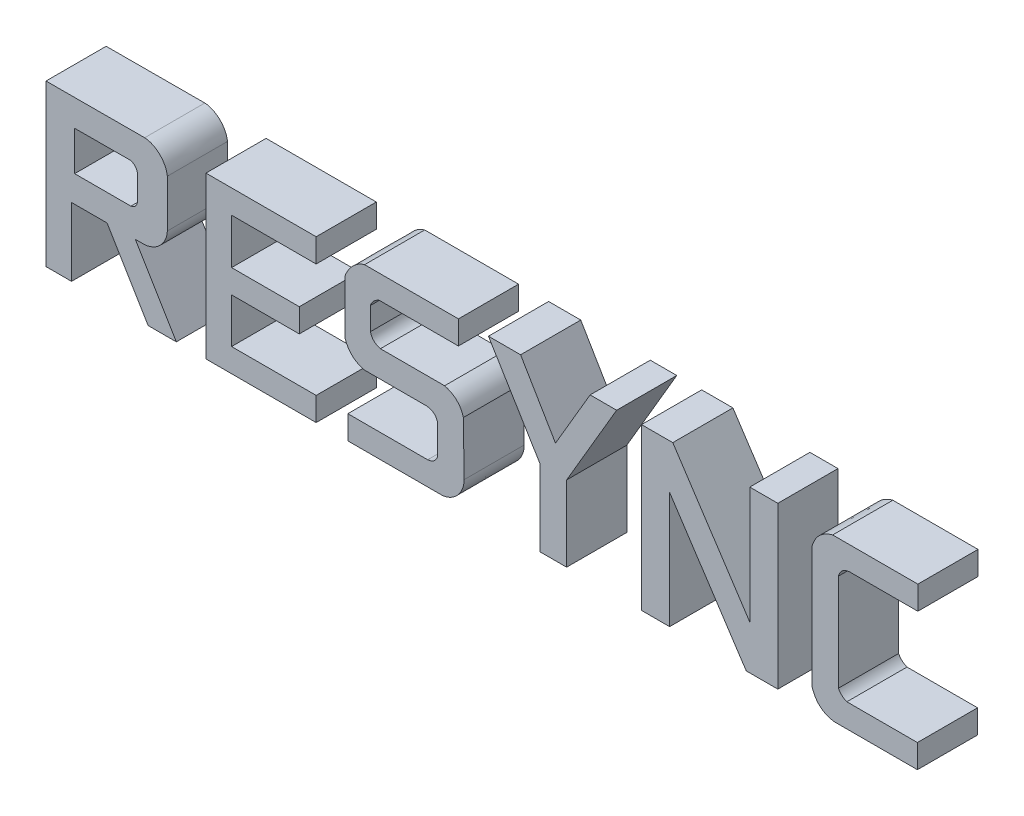
SolidWorks part; units mm, degrees
ref_plane "Front Plane" through (0, 0, 0) normal (0, 0, 1) x (1, 0, 0)
ref_plane "Top Plane" through (0, 0, 0) normal (0, 1, 0) x (1, 0, 0)
ref_plane "Right Plane" through (0, 0, 0) normal (1, 0, 0) x (0, 0, -1)
sketch "Sketch39" plane through (0, 0, 0) normal (0, 0, 1) x (1, 0, 0)
  line L0 (147.6667, 279.75) -> (830.3333, 279.75) construction
  line L1 (297, 531.75) -> (1577, 531.75) construction
  line L2 (-15.0225, 6.9502) -> (-15.0225, 1.4057)
  line L3 (-15.0225, 1.4057) -> (-13.9728, 1.4057)
  line L4 (-13.9728, 1.4057) -> (-13.9728, 3.6779)
  line L5 (-13.9728, 3.6779) -> (-12.9478, 3.6779)
  line L6 (-12.9478, 3.6779) -> (-11.5831, 1.4057)
  line L7 (-11.5831, 1.4057) -> (-10.4121, 1.4057)
  line L8 (-10.4121, 1.4057) -> (-11.7768, 3.6779)
  line L9 (-11.7768, 3.6779) -> (-11.6385, 3.6779)
  line L10 (-10.7883, 4.5476) -> (-10.7883, 6.1322)
  line L11 (-11.6385, 6.9576) -> (-15.0225, 6.9502)
  line L12 (-13.9728, 5.9647) -> (-13.9699, 4.6587)
  line L13 (-13.9699, 4.6587) -> (-12.0989, 4.6587)
  line L14 (-11.885, 4.8692) -> (-11.885, 5.7351)
  line L15 (-12.1205, 5.972) -> (-13.9728, 5.9647)
  line L16 (-9.7048, 6.9576) -> (-9.7048, 1.4057)
  line L17 (-9.7048, 1.4057) -> (-5.8401, 1.4057)
  line L18 (-5.8401, 1.4057) -> (-5.8401, 2.3891)
  line L19 (-5.8401, 2.3891) -> (-8.6526, 2.3891)
  line L20 (-8.6526, 2.3891) -> (-8.6526, 3.6779)
  line L21 (-8.6526, 3.6779) -> (-6.4009, 3.6779)
  line L22 (-6.4009, 3.6779) -> (-6.4009, 4.6624)
  line L23 (-6.4009, 4.6624) -> (-8.6526, 4.6624)
  line L24 (-8.6526, 4.6624) -> (-8.6526, 5.972)
  line L25 (-8.6526, 5.972) -> (-5.8401, 5.972)
  line L26 (-5.8401, 5.972) -> (-5.8401, 6.9576)
  line L27 (-5.8401, 6.9576) -> (-9.7048, 6.9576)
  line L28 (-4.9866, 1.4057) -> (-1.7436, 1.4057)
  line L29 (-0.9222, 2.3209) -> (-0.9432, 4.116)
  line L30 (-1.6562, 4.8018) -> (-3.7908, 4.8018)
  line L31 (-4.0366, 5.0385) -> (-4.0366, 5.7632)
  line L32 (-3.8276, 5.976) -> (-1.1096, 5.976)
  line L33 (-1.1096, 5.976) -> (-1.1096, 6.9576)
  line L34 (-1.1096, 6.9576) -> (-4.3432, 6.9576)
  line L35 (-5.0828, 6.2212) -> (-5.0828, 4.4143)
  line L36 (-4.3432, 3.7217) -> (-2.2708, 3.7217)
  line L37 (-1.9972, 3.5013) -> (-1.9972, 2.5759)
  line L38 (-2.2357, 2.3891) -> (-4.9866, 2.3891)
  line L39 (-4.9866, 2.3891) -> (-4.9866, 1.4057)
  line L40 (-0.3891, 6.9576) -> (1.3981, 4.0225)
  line L41 (1.3981, 4.0225) -> (1.3981, 1.4057)
  line L42 (1.3981, 1.4057) -> (2.4881, 1.4057)
  line L43 (2.4881, 1.4057) -> (2.4881, 3.9919)
  line L44 (2.4881, 3.9919) -> (4.2251, 6.9576)
  line L45 (4.2251, 6.9576) -> (3.1117, 6.9576)
  line L46 (3.1117, 6.9576) -> (2.0173, 5.0892)
  line L47 (2.0173, 5.0892) -> (0.9145, 6.9576)
  line L48 (0.9145, 6.9576) -> (-0.3891, 6.9576)
  line L49 (4.7787, 6.9576) -> (4.7787, 1.4057)
  line L50 (4.7787, 1.4057) -> (5.9124, 1.4057)
  line L51 (5.9124, 1.4057) -> (5.9124, 5.0385)
  line L52 (5.9124, 5.0385) -> (8.3065, 1.4057)
  line L53 (8.3065, 1.4057) -> (9.5107, 1.4057)
  line L54 (9.5107, 1.4057) -> (9.5107, 6.9576)
  line L55 (9.5107, 6.9576) -> (8.377, 6.9576)
  line L56 (8.377, 6.9576) -> (8.377, 3.307)
  line L57 (8.377, 3.307) -> (5.971, 6.9576)
  line L58 (5.971, 6.9576) -> (4.7787, 6.9576)
  line L59 (11.2204, 6.9576) -> (14.1659, 6.9576)
  line L60 (14.1659, 6.9576) -> (14.1659, 5.976)
  line L61 (14.1659, 5.976) -> (11.8028, 5.976)
  line L62 (11.525, 5.7538) -> (11.525, 2.5629)
  line L63 (11.7216, 2.3891) -> (14.1513, 2.3891)
  line L64 (14.1513, 2.3891) -> (14.1513, 1.4057)
  line L65 (14.1513, 1.4057) -> (11.2756, 1.4057)
  line L66 (10.4471, 2.1356) -> (10.4471, 6.2043)
  line L67 (-11.6412, 6.8576) -> (-14.9225, 6.8504)
  line L68 (-14.9225, 6.8504) -> (-14.9225, 1.5057)
  line L69 (-14.9225, 1.5057) -> (-14.0728, 1.5057)
  line L70 (-14.0728, 1.5057) -> (-14.0728, 3.7779)
  line L71 (-14.0728, 3.7779) -> (-12.8913, 3.7779)
  line L72 (-12.8913, 3.7779) -> (-11.5265, 1.5057)
  line L73 (-11.5265, 1.5057) -> (-10.5888, 1.5057)
  line L74 (-10.5888, 1.5057) -> (-11.9535, 3.7779)
  line L75 (-11.9535, 3.7779) -> (-11.6421, 3.7779)
  line L76 (-10.8883, 4.5493) -> (-10.8883, 6.127)
  line L77 (-5.9401, 6.8576) -> (-9.6048, 6.8576)
  line L78 (-9.6048, 6.8576) -> (-9.6048, 1.5057)
  line L79 (-9.6048, 1.5057) -> (-5.9401, 1.5057)
  line L80 (-5.9401, 1.5057) -> (-5.9401, 2.2891)
  line L81 (-5.9401, 2.2891) -> (-8.7526, 2.2891)
  line L82 (-8.7526, 2.2891) -> (-8.7526, 3.7779)
  line L83 (-8.7526, 3.7779) -> (-6.5009, 3.7779)
  line L84 (-6.5009, 3.7779) -> (-6.5009, 4.5624)
  line L85 (-6.5009, 4.5624) -> (-8.7526, 4.5624)
  line L86 (-8.7526, 4.5624) -> (-8.7526, 6.072)
  line L87 (-8.7526, 6.072) -> (-5.9401, 6.072)
  line L88 (-5.9401, 6.072) -> (-5.9401, 6.8576)
  line L89 (-1.8972, 3.5143) -> (-1.8972, 2.5596)
  line L90 (-2.2312, 2.2891) -> (-4.8866, 2.2891)
  line L91 (-4.8866, 2.2891) -> (-4.8866, 1.5057)
  line L92 (-4.8866, 1.5057) -> (-1.7478, 1.5057)
  line L93 (-1.0222, 2.3197) -> (-1.0431, 4.101)
  line L94 (-1.6691, 4.7018) -> (-3.8035, 4.7018)
  line L95 (-4.1366, 5.0243) -> (-4.1366, 5.7792)
  line L96 (-3.845, 6.076) -> (-1.2096, 6.076)
  line L97 (-1.2096, 6.076) -> (-1.2096, 6.8576)
  line L98 (-1.2096, 6.8576) -> (-4.3307, 6.8576)
  line L99 (-4.9828, 6.2047) -> (-4.9828, 4.4296)
  line L100 (-4.3314, 3.8217) -> (-2.2675, 3.8217)
  line L101 (0.8574, 6.8576) -> (-0.2112, 6.8576)
  line L102 (-0.2112, 6.8576) -> (1.4981, 4.0505)
  line L103 (1.4981, 4.0505) -> (1.4981, 1.5057)
  line L104 (1.4981, 1.5057) -> (2.3881, 1.5057)
  line L105 (2.3881, 1.5057) -> (2.3881, 4.019)
  line L106 (2.3881, 4.019) -> (4.0506, 6.8576)
  line L107 (4.0506, 6.8576) -> (3.169, 6.8576)
  line L108 (3.169, 6.8576) -> (2.0177, 4.8919)
  line L109 (2.0177, 4.8919) -> (0.8574, 6.8576)
  line L110 (5.9172, 6.8576) -> (4.8787, 6.8576)
  line L111 (4.8787, 6.8576) -> (4.8787, 1.5057)
  line L112 (4.8787, 1.5057) -> (5.8124, 1.5057)
  line L113 (5.8124, 1.5057) -> (5.8124, 5.372)
  line L114 (5.8124, 5.372) -> (8.3604, 1.5057)
  line L115 (8.3604, 1.5057) -> (9.4107, 1.5057)
  line L116 (9.4107, 1.5057) -> (9.4107, 6.8576)
  line L117 (9.4107, 6.8576) -> (8.477, 6.8576)
  line L118 (8.477, 6.8576) -> (8.477, 2.9735)
  line L119 (8.477, 2.9735) -> (5.9172, 6.8576)
  line L120 (11.2332, 6.8576) -> (14.0659, 6.8576)
  line L121 (14.0659, 6.8576) -> (14.0659, 6.076)
  line L122 (14.0659, 6.076) -> (11.7997, 6.076)
  line L123 (11.425, 5.7674) -> (11.425, 2.5393)
  line L124 (11.7046, 2.2891) -> (14.0513, 2.2891)
  line L125 (14.0513, 2.2891) -> (14.0513, 1.5057)
  line L126 (14.0513, 1.5057) -> (11.2829, 1.5057)
  line L127 (10.5471, 2.1506) -> (10.5471, 6.1901)
  spline S0 degree 3 poles (-11.6385, 3.6779) (-11.1992, 3.7086) (-10.8033, 4.0794) (-10.7883, 4.5476) knots 0 0 0 0 1 1 1 1
  spline S1 degree 3 poles (-10.7883, 6.1322) (-10.8311, 6.5559) (-11.2076, 6.9342) (-11.6385, 6.9576) knots 0 0 0 0 1 1 1 1
  spline S2 degree 2 poles (-12.0989, 4.6587) (-11.9219, 4.6939) (-11.885, 4.8692) knots 0 0 0 1 1 1
  spline S3 degree 2 poles (-11.885, 5.7351) (-11.9286, 5.9229) (-12.1205, 5.972) knots 0 0 0 1 1 1
  spline S4 degree 3 poles (-1.7436, 1.4057) (-1.3804, 1.4351) (-0.9949, 1.7823) (-0.9211, 2.2256) (-0.9222, 2.3209) knots 0 0 0 0 0.786572 1 1 1 1
  spline S5 degree 2 poles (-0.9432, 4.116) (-1.0994, 4.659) (-1.6562, 4.8018) knots 0 0 0 1 1 1
  spline S6 degree 2 poles (-3.7908, 4.8018) (-3.9821, 4.8512) (-4.0366, 5.0385) knots 0 0 0 1 1 1
  spline S7 degree 2 poles (-4.0366, 5.7632) (-3.9851, 5.9195) (-3.8276, 5.976) knots 0 0 0 1 1 1
  spline S8 degree 3 poles (-4.3432, 6.9576) (-4.7111, 6.8668) (-4.9695, 6.562) (-5.0828, 6.2212) knots 0 0 0 0 1 1 1 1
  spline S9 degree 2 poles (-5.0828, 4.4143) (-4.911, 3.8544) (-4.3432, 3.7217) knots 0 0 0 1 1 1
  spline S10 degree 2 poles (-2.2708, 3.7217) (-2.0516, 3.7069) (-1.9972, 3.5013) knots 0 0 0 1 1 1
  spline S11 degree 2 poles (-1.9972, 2.5759) (-2.0542, 2.4054) (-2.2357, 2.3891) knots 0 0 0 1 1 1
  spline S12 degree 2 poles (11.8028, 5.976) (11.5825, 5.9623) (11.525, 5.7538) knots 0 0 0 1 1 1
  spline S13 degree 2 poles (11.525, 2.5629) (11.5888, 2.4355) (11.7216, 2.3891) knots 0 0 0 1 1 1
  spline S14 degree 2 poles (11.2756, 1.4057) (10.6391, 1.4971) (10.4471, 2.1356) knots 0 0 0 1 1 1
  spline S15 degree 2 poles (10.4471, 6.2043) (10.6161, 6.8025) (11.2204, 6.9576) knots 0 0 0 1 1 1
  spline S16 degree 1 poles (-11.6421, 3.7779) (-10.8883, 4.5493) knots 0 0 1 1 construction
  spline S17 degree 1 poles (-10.8883, 6.127) (-11.6412, 6.8576) knots 0 0 1 1 construction
  spline S18 degree 3 poles (-11.6421, 3.7779) (-11.452, 3.792) (-11.0748, 3.9663) (-10.8949, 4.3563) (-10.8883, 4.5493) knots 0.002907 0.002907 0.002907 0.002907 0.500827 0.998747 0.998747 0.998747 0.998747
  spline S19 degree 3 poles (-10.8883, 6.127) (-10.9082, 6.3115) (-11.0949, 6.6696) (-11.4568, 6.8468) (-11.6412, 6.8576) knots 0.004358 0.004358 0.004358 0.004358 0.500968 0.997578 0.997578 0.997578 0.997578
  spline S20 degree 1 poles (-1.8972, 2.5596) (-2.2312, 2.2891) knots 0 0 1 1 construction
  spline S21 degree 1 poles (-1.7478, 1.5057) (-1.0222, 2.3197) knots 0 0 1 1 construction
  spline S22 degree 1 poles (-1.0431, 4.101) (-1.6691, 4.7018) knots 0 0 1 1 construction
  spline S23 degree 1 poles (-3.8035, 4.7018) (-4.1366, 5.0243) knots 0 0 1 1 construction
  spline S24 degree 1 poles (-4.1366, 5.7792) (-3.845, 6.076) knots 0 0 1 1 construction
  spline S25 degree 1 poles (-4.3307, 6.8576) (-4.9828, 6.2047) knots 0 0 1 1 construction
  spline S26 degree 1 poles (-4.9828, 4.4296) (-4.3314, 3.8217) knots 0 0 1 1 construction
  spline S27 degree 1 poles (-2.2675, 3.8217) (-1.8972, 3.5143) knots 0 0 1 1 construction
  spline S28 degree 3 poles (-1.8972, 2.5596) (-1.921, 2.4884) (-1.9979, 2.3472) (-2.1556, 2.2959) (-2.2312, 2.2891) knots -0.045302 -0.045302 -0.045302 -0.045302 0.483486 1.012274 1.012274 1.012274 1.012274
  spline S29 degree 3 poles (-1.7478, 1.5057) (-1.554, 1.5225) (-1.1761, 1.7306) (-1.02, 2.126) (-1.0222, 2.3197) knots 0.003205 0.003205 0.003205 0.003205 0.501603 1 1 1 1
  spline S30 degree 3 poles (-1.0431, 4.101) (-1.0656, 4.1763) (-1.1299, 4.3279) (-1.2627, 4.4936) (-1.4346, 4.6207) (-1.5917, 4.6812) (-1.6691, 4.7018) knots 0.012744 0.012744 0.012744 0.012744 0.25664 0.500537 0.744433 0.98833 0.98833 0.98833 0.98833
  spline S31 degree 3 poles (-3.8035, 4.7018) (-3.8816, 4.722) (-4.0381, 4.7941) (-4.1142, 4.9471) (-4.1366, 5.0243) knots -0.032088 -0.032088 -0.032088 -0.032088 0.5022 1.036488 1.036488 1.036488 1.036488
  spline S32 degree 3 poles (-4.1366, 5.7792) (-4.0932, 5.911) (-3.9755, 6.0292) (-3.845, 6.076) knots -0.048739 -0.048739 -0.048739 -0.048739 1.051963 1.051963 1.051963 1.051963
  spline S33 degree 3 poles (-4.3307, 6.8576) (-4.6282, 6.7796) (-4.8819, 6.4953) (-4.9828, 6.2047) knots 0.011689 0.011689 0.011689 0.011689 0.984046 0.984046 0.984046 0.984046
  spline S34 degree 3 poles (-4.9828, 4.4296) (-4.9579, 4.3519) (-4.8885, 4.1952) (-4.749, 4.0263) (-4.5711, 3.8991) (-4.4105, 3.841) (-4.3314, 3.8217) knots 0.013618 0.013618 0.013618 0.013618 0.257586 0.501553 0.74552 0.989487 0.989487 0.989487 0.989487
  spline S35 degree 3 poles (-2.2675, 3.8217) (-2.1819, 3.8159) (-2.001, 3.7609) (-1.9189, 3.5962) (-1.8972, 3.5143) knots -0.007666 -0.007666 -0.007666 -0.007666 0.511461 1.030587 1.030587 1.030587 1.030587
  spline S36 degree 1 poles (10.5471, 6.1901) (11.2332, 6.8576) knots 0 0 1 1 construction
  spline S37 degree 1 poles (11.7997, 6.076) (11.425, 5.7674) knots 0 0 1 1 construction
  spline S38 degree 1 poles (11.425, 2.5393) (11.7046, 2.2891) knots 0 0 1 1 construction
  spline S39 degree 1 poles (11.2829, 1.5057) (10.5471, 2.1506) knots 0 0 1 1 construction
  spline S40 degree 3 poles (10.5471, 6.1901) (10.5717, 6.2739) (10.6421, 6.4431) (10.7879, 6.6277) (10.9767, 6.7687) (11.1485, 6.835) (11.2332, 6.8576) knots 0.011814 0.011814 0.011814 0.011814 0.25618 0.500547 0.744913 0.98928 0.98928 0.98928 0.98928
  spline S41 degree 3 poles (11.7997, 6.076) (11.7135, 6.0707) (11.5315, 6.0156) (11.4478, 5.8498) (11.425, 5.7674) knots -0.007036 -0.007036 -0.007036 -0.007036 0.512122 1.031281 1.031281 1.031281 1.031281
  spline S42 degree 3 poles (11.425, 2.5393) (11.481, 2.4274) (11.5866, 2.3304) (11.7046, 2.2891) knots -0.082923 -0.082923 -0.082923 -0.082923 1.060321 1.060321 1.060321 1.060321
  spline S43 degree 3 poles (11.2829, 1.5057) (11.1942, 1.519) (11.0111, 1.5689) (10.8114, 1.6981) (10.6541, 1.881) (10.5748, 2.0618) (10.5471, 2.1506) knots 0.005889 0.005889 0.005889 0.005889 0.251502 0.497115 0.742728 0.988341 0.988341 0.988341 0.988341
  dimension "D1" = 0.1
extrude "Boss-Extrude8" add sketch "Sketch39" along normal blind 2 contours L76 S19 L67 L68 L69 L70 L71 L72 L73 L74 L75 S18 S3 L14 S2 L13 L12 L15 | L87 L88 L77 L78 L79 L80 L81 L82 L83 L84 L85 L86 | L100 S35 L89 S28 L90 L91 L92 S29 L93 S30 L94 S31 L95 S32 L96 L97 L98 S33 L99 S34 | L118 L119 L110 L111 L112 L113 L114 L115 L116 L117 | S43 L126 L125 L124 S42 L123 S41 L122 L121 L120 S40 L127 | L109 L101 L102 L103 L104 L105 L106 L107 L108
